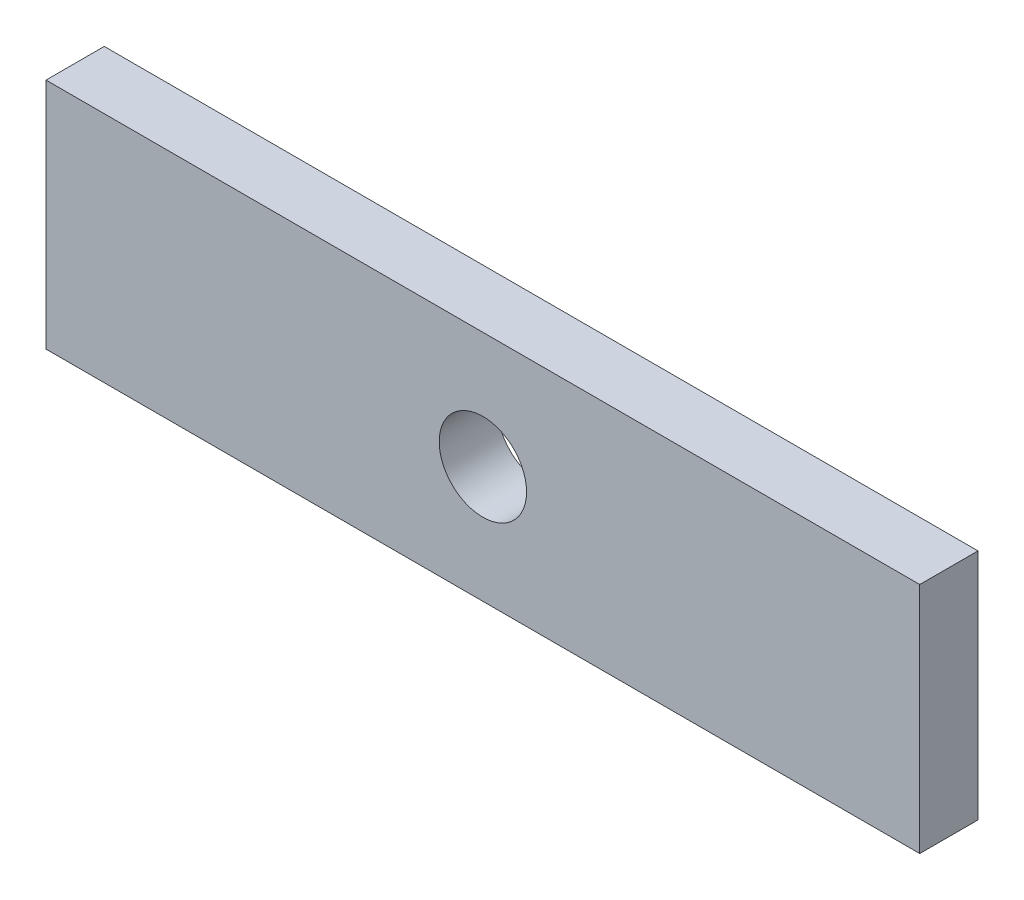
SolidWorks part; units mm, degrees
ref_plane "Alzado" through (0, 0, 0) normal (0, 0, 1) x (1, 0, 0)
ref_plane "Planta" through (0, 0, 0) normal (0, 1, 0) x (1, 0, 0)
ref_plane "Vista lateral" through (0, 0, 0) normal (1, 0, 0) x (0, 0, -1)
sketch "Croquis1" plane through (0, 0, 0) normal (0, 0, 1) x (1, 0, 0)
  line L0 (0, 20) -> (75, 20) construction
  line L1 (0, 0) -> (150, 0)
  line L2 (0, 0) -> (0, 40)
  line L3 (0, 40) -> (150, 40)
  line L4 (150, 0) -> (150, 40)
  line L5 (75, 20) -> (75, 40) construction
  circle A0 centre (75, 20) radius 7.5
  dimension "DIAMETRO" = 15
  dimension "LARGO" = 150
  dimension "ALTO" = 40
extrude "Saliente-Extruir1" add sketch "Croquis1" along normal blind 10
